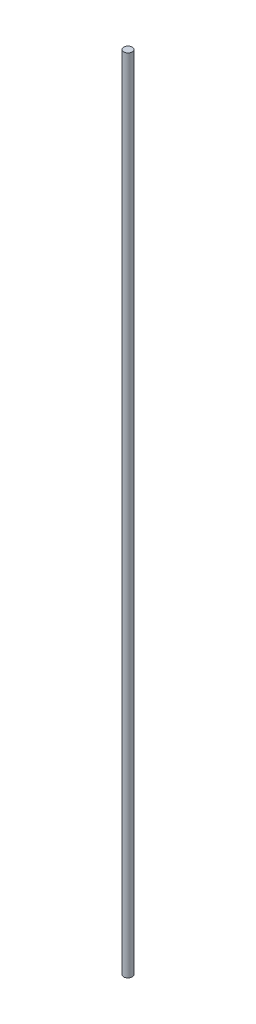
SolidWorks part; units mm, degrees
material "304不锈钢"
ref_plane "前视基准面" through (0, 0, 0) normal (0, 0, 1) x (1, 0, 0)
ref_plane "上视基准面" through (0, 0, 0) normal (0, 1, 0) x (1, 0, 0)
ref_plane "右视基准面" through (0, 0, 0) normal (1, 0, 0) x (0, 0, -1)
sketch "草图1" plane through (0, 0, 0) normal (0, 1, 0) x (1, 0, 0)
  circle A0 centre (0, 0) radius 4
  dimension "D1" = 8
extrude "丝杆" add sketch "草图1" along normal blind 750
cosmetic thread "装饰螺纹线1" parameters "D2"=6.647
